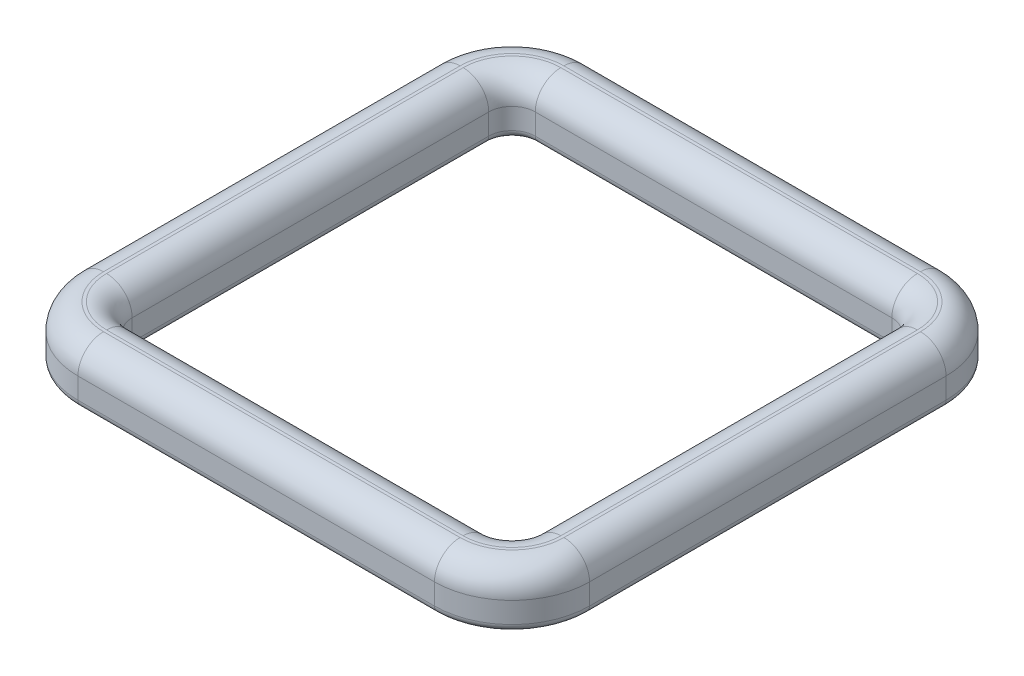
SolidWorks part; units mm, degrees
ref_plane "Front Plane" through (0, 0, 0) normal (0, 0, 1) x (1, 0, 0)
ref_plane "Top Plane" through (0, 0, 0) normal (0, 1, 0) x (1, 0, 0)
ref_plane "Right Plane" through (0, 0, 0) normal (1, 0, 0) x (0, 0, -1)
sketch "Sketch1" plane through (0, 0, 0) normal (0, 1, 0) x (1, 0, 0)
  line L0 (-8.89, 3.81) -> (-8.89, 62.23)
  line L1 (3.81, 0) -> (62.23, 0)
  line L2 (0, 3.81) -> (0, 62.23)
  line L3 (3.81, 66.04) -> (62.23, 66.04)
  line L4 (66.04, 3.81) -> (66.04, 62.23)
  line L5 (3.81, 74.93) -> (62.23, 74.93)
  line L6 (74.93, 3.81) -> (74.93, 62.23)
  line L7 (3.81, -8.89) -> (62.23, -8.89)
  arc A0 (3.81, 0) -> (0, 3.81) centre (3.81, 3.81) cw
  arc A1 (62.23, 0) -> (66.04, 3.81) centre (62.23, 3.81) ccw
  arc A2 (62.23, 66.04) -> (66.04, 62.23) centre (62.23, 62.23) cw
  arc A3 (0, 62.23) -> (3.81, 66.04) centre (3.81, 62.23) cw
  arc A4 (-8.89, 62.23) -> (3.81, 74.93) centre (3.81, 62.23) cw
  arc A5 (62.23, 74.93) -> (74.93, 62.23) centre (62.23, 62.23) cw
  arc A6 (62.23, -8.89) -> (74.93, 3.81) centre (62.23, 3.81) ccw
  arc A7 (3.81, -8.89) -> (-8.89, 3.81) centre (3.81, 3.81) cw
  point P7 (0, 0)
  point P10 (66.04, 0)
  point P15 (0, 66.04)
  dimension "D3" = 3.81
  dimension "D1" = 66.04
  dimension "D2" = 66.04
  dimension "D4" = 8.89
extrude "Boss-Extrude1" add sketch "Sketch1" along normal blind 8.89
fillet "Fillet1" radius 4.191 16 edges at (33.02, 8.89, 0) (64.9241, 8.89, -1.1159) (66.04, 8.89, -33.02) (64.9241, 8.89, -64.9241) (33.02, 8.89, -66.04) (1.1159, 8.89, -64.9241) (0, 8.89, -33.02) (1.1159, 8.89, -1.1159) (-8.89, 8.89, -33.02) (-5.1703, 8.89, -71.2103) (33.02, 8.89, -74.93) (71.2103, 8.89, -71.2103) (74.93, 8.89, -33.02) (71.2103, 8.89, 5.1703) (33.02, 8.89, 8.89) (-5.1703, 8.89, 5.1703)
fillet "Fillet2" radius 1.27 16 edges at (1.1159, 0, -64.9241) (33.02, 0, -66.04) (64.9241, 0, -64.9241) (66.04, 0, -33.02) (64.9241, 0, -1.1159) (33.02, 0, 0) (1.1159, 0, -1.1159) (0, 0, -33.02) (33.02, 0, 8.89) (71.2103, 0, 5.1703) (74.93, 0, -33.02) (71.2103, 0, -71.2103) (33.02, 0, -74.93) (-5.1703, 0, -71.2103) (-8.89, 0, -33.02) (-5.1703, 0, 5.1703)
